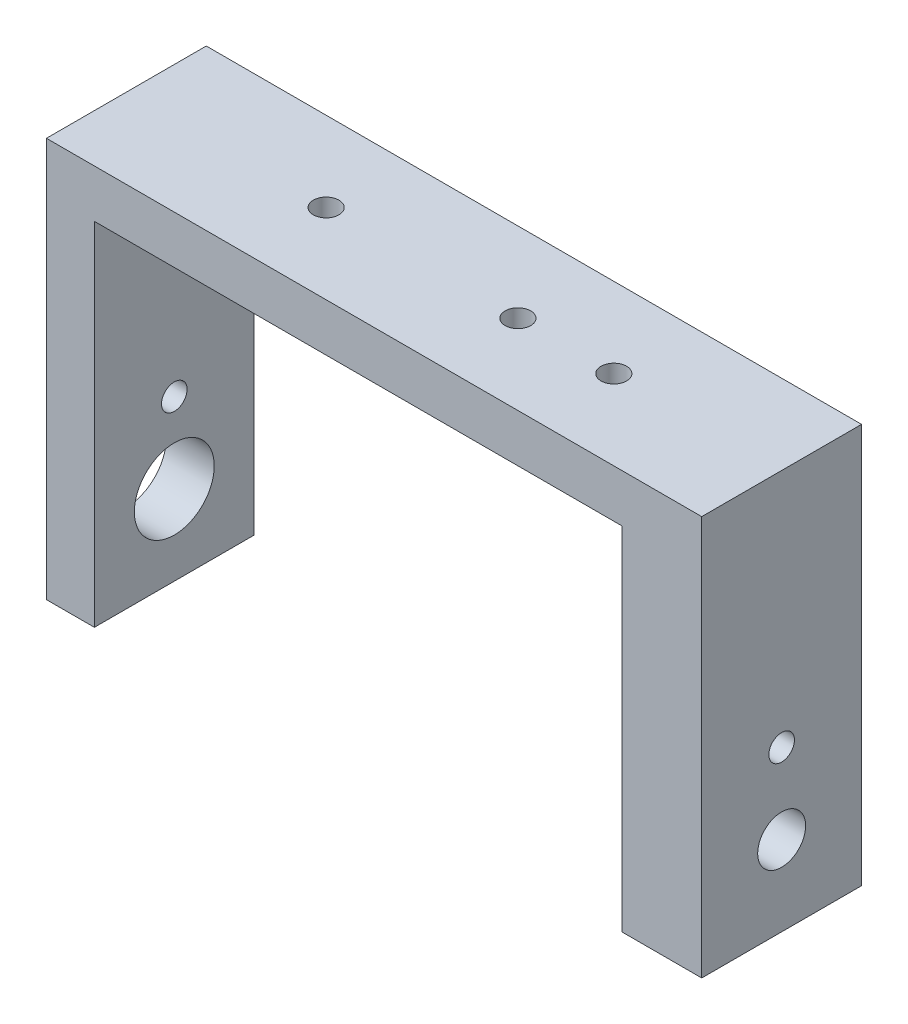
SolidWorks part; units mm, degrees
ref_plane "Front Plane" through (0, 0, 0) normal (0, 0, 1) x (1, 0, 0)
ref_plane "Top Plane" through (0, 0, 0) normal (0, 1, 0) x (1, 0, 0)
ref_plane "Right Plane" through (0, 0, 0) normal (1, 0, 0) x (0, 0, -1)
sketch "Sketch1" plane through (0, 0, 0) normal (0, 0, 1) x (1, 0, 0)
  line L1 (-16.5, 11) -> (16.5, 11)
  line L2 (-16.5, 11) -> (-16.5, -11)
  line L3 (-16.5, -11) -> (16.5, -11)
  line L4 (16.5, 11) -> (16.5, -11)
  line L5 (-16.5, 11) -> (16.5, -11) construction
  line L6 (-16.5, -11) -> (16.5, 11) construction
  line L7 (-19.5, -14) -> (19.5, -14)
  line L8 (-19.5, -14) -> (-19.5, 14)
  line L9 (-19.5, 14) -> (19.5, 14)
  line L10 (19.5, -14) -> (19.5, 14)
  line L11 (-19.5, -14) -> (19.5, 14) construction
  line L12 (-19.5, 14) -> (19.5, -14) construction
  line L13 (-19.5, -14) -> (21.5, -14)
  line L14 (-19.5, -14) -> (-19.5, 14)
  line L15 (-19.5, 14) -> (21.5, 14)
  line L16 (21.5, -14) -> (21.5, 14)
  point P0 (0, 0)
  point P6 (0, 0)
  dimension "D1" = 33
  dimension "D2" = 3
  dimension "D3" = 3
  dimension "D4" = 22
  dimension "D5" = 5
sketch "Sketch2" plane through (0, 0, 0) normal (0, 0, 1) x (1, 0, 0)
  line L0 (-16.5, -11) -> (-19.5, -11)
  line L1 (-19.5, -14) -> (-19.5, 14) construction
  line L2 (-19.5, -11) -> (-19.5, 14)
  line L3 (21.5, 14) -> (-19.5, 14)
  line L4 (16.5, -11) -> (21.5, -11)
  line L6 (21.5, -14) -> (21.5, 14) construction
  line L7 (16.5, -11) -> (16.5, 11)
  line L8 (16.5, 11) -> (-16.5, 11)
  line L9 (-16.5, 11) -> (-16.5, -11)
  line L10 (21.5, -11) -> (21.5, 14)
extrude "Boss-Extrude1" add sketch "Sketch2" along normal blind 10
sketch "Sketch3" plane through (-19.5, 0, 0) normal (-1, 0, 0) x (0, 0, 1)
  line L0 (5, 14) -> (5, -11) construction
  line L1 (10, 14) -> (0, 14) construction
  line L2 (10, -11) -> (0, -11) construction
  line L3 (0, -6) -> (10, -6)
  line L4 (10, 14) -> (10, -11) construction
  line L5 (0, -1) -> (10, -1)
  point P11 (5, -6)
  point P14 (5, -1)
  dimension "D1" = 5
  dimension "D2" = 5
sketch "Sketch4" plane through (-19.5, 0, 0) normal (-1, 0, 0) x (0, 0, 1)
  circle A0 centre (5, -6) radius 1.5
  circle A1 centre (5, -1) radius 0.8
extrude "Cut-Extrude1" cut sketch "Sketch4" against normal through all
sketch "Sketch5" plane through (0, 14, 0) normal (0, 1, 0) x (1, 0, 0)
  line L0 (-19.5, -5) -> (21.5, -5) construction
  line L1 (-19.5, -10) -> (-19.5, 0) construction
  line L2 (21.5, -10) -> (21.5, 0) construction
  line L3 (-7, 0) -> (-7, -10)
  line L4 (21.5, -10) -> (-19.5, -10) construction
  line L5 (11, 0) -> (11, -10)
  point P11 (-7, -5)
  point P14 (11, -5)
  point P16 (5, -5)
  point P17 (0, 0)
  dimension "D1" = 18
  dimension "D3" = 10.5
  dimension "D4" = 12
sketch "Sketch6" plane through (0, 14, 0) normal (0, 1, 0) x (1, 0, 0)
  line L0 (11, 0) -> (11, -10) construction
  circle A0 centre (-7, -5) radius 0.8
  circle A1 centre (11, -5) radius 0.8
  circle A2 centre (5, -5) radius 0.8
extrude "Cut-Extrude2" cut sketch "Sketch6" against normal through all
sketch "Sketch7" plane through (16.5, 0, 0) normal (-1, 0, 0) x (0, 0, 1)
  line L0 (0, -11) -> (0, 12)
  line L1 (0, 11) -> (0, -11) construction
  line L2 (10, -11) -> (0, -11) construction
  line L3 (0, 12) -> (10, 12)
  line L4 (10, 11) -> (10, -11) construction
  point P5 (1, -11)
  point P6 (9, -11)
  point P13 (3, 12)
  point P14 (7, 12)
  point P15 (1, -1)
  point P16 (9, -1)
  dimension "D1" = 1
  dimension "D2" = 1
  dimension "D3" = 3
  dimension "D4" = 3
  dimension "D5" = 10
  dimension "D6" = 1
  dimension "D7" = 10
  dimension "D8" = 1
  dimension "D9" = 13
sketch "Sketch8" plane through (16.5, 0, 0) normal (-1, 0, 0) x (0, 0, 1)
  line L0 (1, -1) -> (1, -11)
  line L1 (3, 12) -> (7, 12)
  line L2 (3, 12) -> (1, -1)
  line L3 (1, -11) -> (9, -11)
  line L5 (7, 12) -> (9, -1)
  line L6 (9, -1) -> (9, -11)
extrude "Cut-Extrude3" cut sketch "Sketch8" against normal blind 2
sketch "Sketch9" plane through (-19.5, 0, 0) normal (-1, 0, 0) x (0, 0, 1)
  circle A0 centre (5, -6) radius 2.5
extrude "Cut-Extrude4" cut sketch "Sketch9" against normal blind 10
